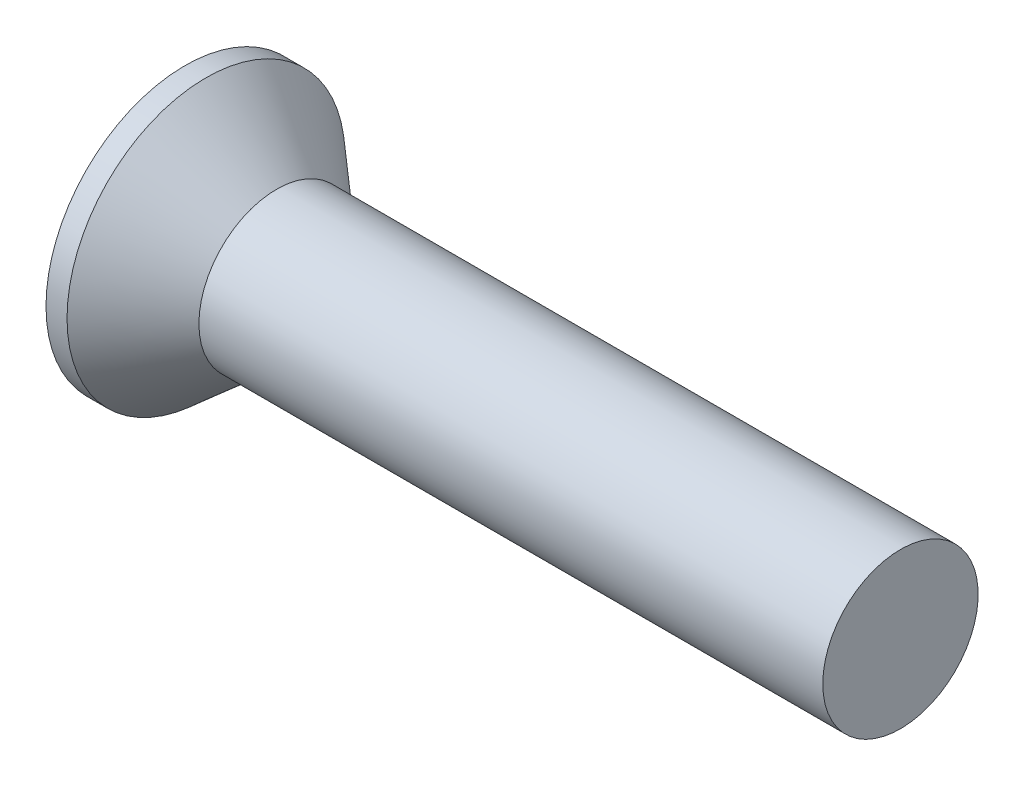
SolidWorks part; units mm, degrees
revolve "Base-Revolve" add sketch "BodySke" angle 360 about L5
sketch "BodySke" plane through (0, 0, 0) normal (0, 0, 1) x (1, 0, 0)
  line L0 (0, 0) -> (0, 4.318)
  line L1 (0, 4.318) -> (0.6533, 4.318)
  line L2 (2.8448, 2.413) -> (22.225, 2.413)
  line L3 (22.225, 2.413) -> (22.225, 0)
  line L4 (22.225, 0) -> (0, 0)
  line L5 (-6.35, 0) -> (82.55, 0) construction
  line L6 (2.8448, -2.413) -> (22.225, -2.413) construction
  line L7 (0.6533, -4.318) -> (2.8448, -2.413) construction
  line L8 (0.6533, 4.318) -> (2.8448, 2.413)
  line L9 (0, -4.318) -> (0.6533, -4.318) construction
  line L10 (3.6373, 4.0005) -> (3.6373, -5.5245) construction
  line L11 (15.875, 6.35) -> (15.875, -3.175) construction
  dimension "Diameter" = 4.826
  dimension "Length" = 22.225
  dimension "Head_ht" = 2.8448
  dimension "Head_dia" = 8.636
  dimension "Head_ang" = 82
  dimension "D6" = 0.6533
  dimension "Advance" = 0.7925
cosmetic thread "ThreadCosmetic" [suppressed] parameters "Thread_length"=6.35, "Thread_minor"=3.8811
extrude "Slot" [suppressed] cut sketch "Sketch2" against normal blind 1.3462
sketch "Sketch2" plane through (0, 0, 0) normal (-1, 0, 0) x (0, 0, 1)
  line L0 (-4.318, -0.762) -> (4.318, -0.762)
  line L1 (-4.318, -0.762) -> (-4.318, 0.762)
  line L2 (4.318, 0.762) -> (-4.318, 0.762)
  line L3 (4.318, 0.762) -> (4.318, -0.762)
  dimension "Slot_width" = 1.524
  dimension "D1" = 0.762
  dimension "D2" = 8.636
  dimension "D3" = 4.318
ref_plane "Plane1" through (0, 0, 0) normal (0, 0, 1) x (1, 0, 0)
ref_plane "Plane2" through (0, 0, 0) normal (0, 1, 0) x (1, 0, 0)
ref_plane "Plane3" through (0, 0, 0) normal (1, 0, 0) x (0, 0, -1)
other "Configuration Table"
sketch "Sketch3" plane through (0, 0, 0) normal (-1, 0, 0) x (0, 0, 1)
  line L0 (-0.6096, 3.4163) -> (0.6096, 3.4163)
  line L1 (0.6096, 3.4163) -> (0.6096, -3.4163)
  line L2 (0.6096, -3.4163) -> (-0.6096, -3.4163)
  line L3 (-0.6096, -3.4163) -> (-0.6096, 3.4163)
  dimension "Cross_dia" = 6.8326
  dimension "Cross_width" = 1.2192
  dimension "D1" = 3.4163
  dimension "D2" = 0.6096
ref_plane "Plane4" through (3.9624, 0, 0) normal (-1, 0, 0) x (0, 0, 1)
sketch "Sketch4" plane through (3.9624, 0, 0) normal (-1, 0, 0) x (0, 0, 1)
  line L0 (-0.3048, 0.3048) -> (0.3048, 0.3048)
  line L3 (0.3048, 0.3048) -> (0.3048, -0.3048)
  line L4 (0.3048, -0.3048) -> (-0.3048, -0.3048)
  line L5 (-0.3048, -0.3048) -> (-0.3048, 0.3048)
  dimension "D2" = 0.6096
  dimension "D1" = 0.6096
  dimension "D3" = 0.3048
  dimension "D4" = 0.3048
loft "Cross" [suppressed] cut profiles "Sketch3", "Sketch4"
pattern_circular "CirPattern1" [suppressed] count 2 every 90 about axis through (-6.35, 0, 0) along (1, 0, 0)
sketch "ThdSchSke" plane through (0, 0, 0) normal (0, 0, 1) x (1, 0, 0)
  line L0 (15.875, -1.9406) -> (15.5442, -2.413)
  line L1 (15.875, -1.9406) -> (16.2058, -2.413)
  line L2 (16.2058, -2.413) -> (16.2058, -3.0162)
  line L3 (-3.175, 0) -> (5.1513, 0) construction
  line L5 (16.2058, -3.0162) -> (15.5442, -3.0162)
  line L6 (15.5442, -3.0162) -> (15.5442, -2.413)
  line L7 (0, 4.318) -> (0, -4.318) construction
  dimension "Diameter" = 4.826
  dimension "Thread_minor" = 3.8811
revolve "ThreadSchematic" [suppressed] cut sketch "ThdSchSke" angle 360 about L3
pattern_linear "ThdSchPat" [suppressed]
equation "\"D1@Sketch3\" = \"Cross_dia@Sketch3\" / 2"
equation "\"D2@Sketch3\" = \"Cross_width@Sketch3\" / 2"
equation "\"D1@Sketch4\" = \"Cross_width@Sketch3\" *.5"
equation "\"D2@Sketch4\" = \"D1@Sketch4\""
equation "\"D4@Sketch4\" = \"D2@Sketch4\" / 2"
equation "\"D3@Sketch4\" = \"D1@Sketch4\" / 2"
equation "\"D1@Sketch2\" = \"Slot_width@Sketch2\" / 2"
equation "\"D2@Sketch2\" = \"Head_dia@BodySke\""
equation "\"D3@Sketch2\" = \"D2@Sketch2\" / 2"
equation "\"Thread_length@ThreadCosmetic\" = ((sgn( (\"Length@BodySke\" - \"Advance@BodySke\" - \"Head_ht@BodySke\" ) - \"Thread_nom@BodySke\" )-1)*( (\"Length@BodySke\" - \"Advance@BodySke\" - \"Head_ht@BodySke\" ) - \"Thread_nom@BodySke\" ))/-2+ \"Thread_nom@BodySke\""
equation "\"Thread_minor@ThdSchSke\" = \"Thread_minor@ThreadCosmetic\""
equation "\"Diameter@ThdSchSke\" = \"Diameter@BodySke\""
equation "\"Overcut@ThdSchSke\" = \"Diameter@BodySke\" * 1.25"
equation "\"Start@ThdSchSke\" = 0.000001 + \"Length@BodySke\" - \"Thread_length@ThreadCosmetic\"  '---Countersunk---"
equation "\"Num_threads@ThdSchPat\" = int( \"Thread_length@ThreadCosmetic\" / \"Advance@BodySke\" + 0.999 )  + 1"
equation "\"Advance@ThdSchPat\" = \"Thread_length@ThreadCosmetic\" /  (\"Num_threads@ThdSchPat\" - 1) 'relax it"
